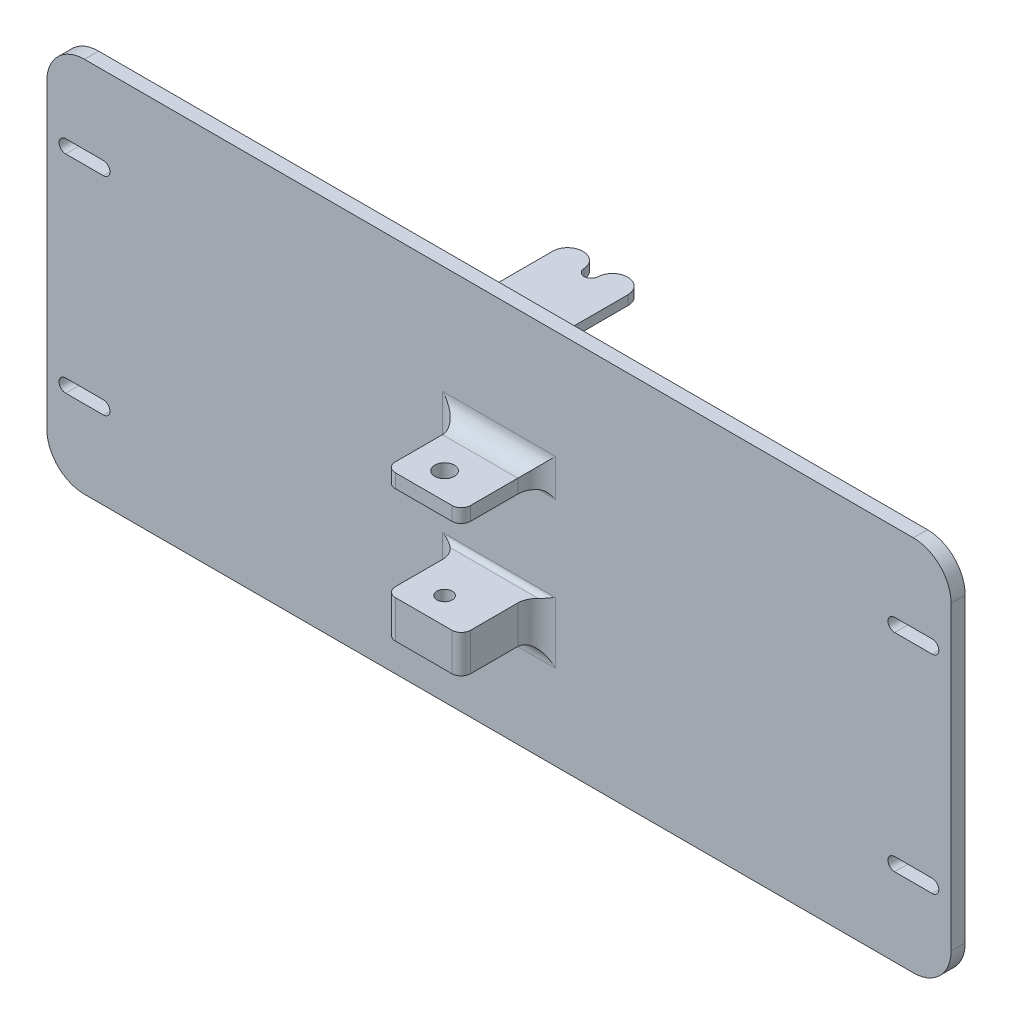
SolidWorks part; units mm, degrees
material "6061-T6 (SS)"
ref_plane "Front" through (0, 0, 0) normal (0, 0, 1) x (1, 0, 0)
ref_plane "Top" through (0, 0, 0) normal (0, 1, 0) x (1, 0, 0)
ref_plane "Right" through (0, 0, 0) normal (1, 0, 0) x (0, 0, -1)
sketch "Sketch1" plane through (0, 0, 0) normal (0, 0, 1) x (1, 0, 0)
  line L1 (-152.4, 63.5) -> (152.4, 63.5)
  line L2 (-152.4, 63.5) -> (-152.4, -63.5)
  line L3 (-152.4, -63.5) -> (152.4, -63.5)
  line L4 (152.4, 63.5) -> (152.4, -63.5)
  dimension "D1" = 152.4
  dimension "D2" = 304.8
  dimension "D3" = 63.5
  dimension "D4" = 127
extrude "Boss-Extrude1" add sketch "Sketch1" along normal blind 4.7625
sketch "Sketch2" plane through (0, 0, 0) normal (0, 0, -1) x (-1, 0, 0)
  line L0 (-12.7, 53.975) -> (12.7, 53.975) construction
  line L1 (0, 63.5) -> (0, -63.5) construction
  line L2 (-152.4, 63.5) -> (152.4, 63.5) construction
  line L3 (152.4, -63.5) -> (-152.4, -63.5) construction
  line L4 (-152.4, 0) -> (152.4, 0) construction
  line L5 (-12.7, 52.3875) -> (12.7, 52.3875)
  line L6 (-12.7, 52.3875) -> (-12.7, 55.5625)
  line L7 (-12.7, 55.5625) -> (12.7, 55.5625)
  line L8 (12.7, 52.3875) -> (12.7, 55.5625)
  line L9 (-152.4, -63.5) -> (-152.4, 63.5) construction
  line L10 (152.4, 63.5) -> (152.4, -63.5) construction
  line L11 (-12.7, -53.975) -> (12.7, -53.975) construction
  line L12 (12.7, -52.3875) -> (12.7, -55.5625)
  line L13 (-12.7, -55.5625) -> (12.7, -55.5625)
  line L14 (-12.7, -52.3875) -> (-12.7, -55.5625)
  line L15 (-12.7, -52.3875) -> (12.7, -52.3875)
  dimension "D1" = 3.175
  dimension "D2" = 25.4
  dimension "D3" = 12.7
  dimension "D4" = 53.975
extrude "Boss-Extrude2" add sketch "Sketch2" along normal blind 31.115
sketch "Sketch3" plane through (0, 0, 0) normal (0, 1, 0) x (1, 0, 0)
  line L0 (12.7, 31.115) -> (-12.7, 31.115) construction
  line L1 (0, 0) -> (0, 22.9508) construction
  line L2 (2.3813, 26.3525) -> (2.3813, 31.115)
  line L3 (2.3813, 31.115) -> (-2.3813, 31.115)
  line L4 (-2.3813, 31.115) -> (-2.3813, 26.3525)
  arc A1 (-2.3813, 26.3525) -> (2.3813, 26.3525) centre (0, 26.3525) ccw
  point P2 (0, 31.115)
  dimension "D2" = 2.3813
  dimension "D1" = 4.7625
  dimension "D3" = 4.7625
  dimension "D4" = 4.7625
extrude "Cut-Extrude1" cut sketch "Sketch3" against normal mid plane 127
fillet "Fillet1" radius 5.08 8 edges at (-2.3813, -53.975, -31.115) (2.3813, -53.975, -31.115) (-2.3813, 53.975, -31.115) (2.3813, 53.975, -31.115) (12.7, -53.975, -31.115) (-12.7, -53.975, -31.115) (-12.7, 53.975, -31.115) (12.7, 53.975, -31.115)
sketch "Sketch4" [suppressed] plane through (0, 0, 0) normal (0, 0, -1) x (-1, 0, 0)
  line L0 (0, 63.5) -> (0, -63.5) construction
  line L1 (-152.4, 63.5) -> (152.4, 63.5) construction
  line L2 (152.4, -63.5) -> (-152.4, -63.5) construction
  line L3 (-152.4, 0) -> (152.4, 0) construction
  line L4 (-60.325, 19.05) -> (-47.625, 19.05)
  line L5 (-60.325, 19.05) -> (-60.325, -19.05)
  line L6 (-60.325, -19.05) -> (-47.625, -19.05)
  line L7 (-47.625, 19.05) -> (-47.625, -19.05)
  line L8 (-152.4, -63.5) -> (-152.4, 63.5) construction
  line L9 (152.4, 63.5) -> (152.4, -63.5) construction
  line L10 (-53.975, 19.05) -> (-53.975, -19.05) construction
  line L11 (53.975, 19.05) -> (53.975, -19.05) construction
  line L12 (47.625, 19.05) -> (47.625, -19.05)
  line L13 (60.325, -19.05) -> (47.625, -19.05)
  line L14 (60.325, 19.05) -> (60.325, -19.05)
  line L15 (60.325, 19.05) -> (47.625, 19.05)
  dimension "D1" = 12.7
  dimension "D2" = 38.1
  dimension "D3" = 19.05
  dimension "D4" = 53.975
hole_wizard "#8-32 Tapped Hole1" positions "Sketch6" profile "Sketch5" tap size "#8-32" standard "Ansi Inch"
sketch "Sketch6" plane through (0, 0, 0) normal (0, 0, -1) x (-1, 0, 0)
  line L0 (-152.4, -63.5) -> (-152.4, 63.5) construction
  line L1 (-152.4, 63.5) -> (152.4, 63.5) construction
  point P0 (-139.7, 34.925)
  dimension "D1" = 12.7
  dimension "D2" = 28.575
sketch "Sketch5" plane through (139.7, 34.925, 0) normal (1, 0, 0) x (0, 1, 0)
  line L0 (0, 0) -> (0, 3.175)
  line L1 (0, 3.175) -> (1.7272, 3.175)
  line L2 (1.7272, 3.175) -> (1.7272, 0)
  line L5 (1.7272, 0) -> (0, 0)
  line L11 (0, -6.35) -> (0, 107.95) construction
  dimension "Thread Major Dia." = 3.4544
  dimension "Thru Tap Drill Depth" = 3.175
pattern_linear "LPattern1" [suppressed] count 2 spacing 279.4 count 2 spacing 69.85
fillet "Fillet2" radius 12.7 4 edges at (152.4, -63.5, 2.3813) (-152.4, -63.5, 2.3813) (-152.4, 63.5, 2.3813) (152.4, 63.5, 2.3813)
fillet "Fillet4" radius 6.35 8 edges at (12.7, -53.975, 0) (0, -52.3875, 0) (-12.7, -53.975, 0) (0, -55.5625, 0) (12.7, 53.975, 0) (0, 55.5625, 0) (-12.7, 53.975, 0) (0, 52.3875, 0)
sketch "Sketch7" plane through (0, 0, 0) normal (0, 0, -1) x (-1, 0, 0)
  line L0 (-146.05, 34.925) -> (-133.35, 34.925) construction
  line L1 (-146.05, 37.1475) -> (-133.35, 37.1475)
  line L2 (-146.05, 32.7025) -> (-133.35, 32.7025)
  line L4 (-139.7, 63.5) -> (139.7, 63.5) construction
  arc A0 (-146.05, 37.1475) -> (-146.05, 32.7025) centre (-146.05, 34.925) ccw
  arc A1 (-133.35, 32.7025) -> (-133.35, 37.1475) centre (-133.35, 34.925) ccw
  point P2 (-139.7, 34.925)
  dimension "D1" = 139.7
  dimension "D3" = 2.2225
  dimension "D2" = 28.575
  dimension "D4" = 12.7
extrude "Cut-Extrude2" cut sketch "Sketch7" against normal up to next (4.7625 mm away)
pattern_linear "LPattern2" count 2 spacing 279.4 along (-1, 0, 0) count 2 spacing 69.85 along (0, -1, 0) of "Cut-Extrude2"
sketch "Sketch8" plane through (0, 0, 4.7625) normal (0, 0, 1) x (1, 0, 0)
  line L0 (-152.4, 0) -> (152.4, 0) construction
  line L1 (-152.4, 50.8) -> (-152.4, -50.8) construction
  line L2 (152.4, -50.8) -> (152.4, 50.8) construction
  line L3 (0, -63.5) -> (0, 63.5) construction
  line L4 (-139.7, -63.5) -> (139.7, -63.5) construction
  line L5 (139.7, 63.5) -> (-139.7, 63.5) construction
  line L7 (-12.7, -28.5433) -> (12.7, -28.5433)
  line L8 (-12.7, -28.5433) -> (-12.7, -15.8432)
  line L9 (-12.7, -15.8432) -> (12.7, -15.8432)
  line L10 (12.7, -28.5433) -> (12.7, -15.8432)
  line L11 (-12.7, 15.9512) -> (12.7, 15.9512)
  line L12 (-12.7, 15.9512) -> (-12.7, 20.5867)
  line L13 (-12.7, 20.5867) -> (12.7, 20.5867)
  line L14 (12.7, 15.9512) -> (12.7, 20.5867)
  dimension "D1" = 12.7
  dimension "D2" = 4.6355
  dimension "D3" = 31.7944
  dimension "D4" = 15.8432
  dimension "D5" = 25.4
  dimension "D6" = 25.4
  dimension "D7" = 12.7
  dimension "D8" = 12.7
extrude "Boss-Extrude3" add sketch "Sketch8" along normal blind 25.4
sketch "Sketch9" plane through (0, 20.5867, 0) normal (0, 1, 0) x (1, 0, 0)
  line L1 (0, 0) -> (-7.8462, -62.3715) construction
  line L2 (12.7, -4.7625) -> (-12.7, -4.7625) construction
  line L4 (0.8497, -0.1069) -> (-6.9965, -62.4784) construction
  line L5 (12.7, -30.1625) -> (-12.7, -30.1625) construction
  circle A0 centre (-1.8129, -21.2725) radius 3.302
  dimension "D2" = 0.8564
  dimension "D1" = 8.89
  dimension "D4" = 6.604
  dimension "D3" = 97.17
extrude "Cut-Extrude3" cut sketch "Sketch9" against normal up to next
hole_wizard "13/64 (0.20313) Diameter Hole1" positions "Sketch11" profile "Sketch10" hole size "13/64" standard "Ansi Inch"
sketch "Sketch11" plane through (0, -15.8432, 0) normal (0, 1, 0) x (-1, 0, 0)
  line L0 (-12.7, 30.1625) -> (12.7, 30.1625) construction
  line L1 (-12.7, 30.1625) -> (-12.7, 4.7625) construction
  point P0 (1.8129, 21.2725)
  dimension "D1" = 8.89
  dimension "D2" = 14.5129
sketch "Sketch10" plane through (-1.8129, -15.8432, 21.2725) normal (1, 0, 0) x (0, 0, 1)
  line L0 (0, 0) -> (0, 10.6179)
  line L1 (0, 10.6179) -> (2.5798, 9.0678)
  line L2 (2.5798, 9.0678) -> (2.5798, 0)
  line L5 (2.5798, 0) -> (0, 0)
  line L10 (0, 10.6179) -> (-2.5798, 9.0678) construction
  line L11 (0, -6.35) -> (0, 107.95) construction
  dimension "Hole Dia." = 5.1595
  dimension "Hole Depth" = 9.0678
  dimension "Drill Angle" = 118
fillet "Fillet5" radius 6.35 4 edges at (12.7, -22.1933, 4.7625) (12.7, 18.269, 4.7625) (-12.7, 18.2689, 4.7625) (-12.7, -22.1932, 4.7625)
fillet "Fillet6" radius 3.175 4 edges at (-12.7, 18.2689, 30.1625) (12.7, 18.2689, 30.1625) (-12.7, -22.1932, 30.1625) (12.7, -22.1932, 30.1625)
fillet "Fillet7" radius 1.5875 2 edges at (0, 15.9512, 4.7625) (0, -15.8432, 4.7625)
sketch "Sketch12" plane through (0, 0, 4.7625) normal (0, 0, 1) x (1, 0, 0)
  line L0 (131.1275, 34.925) -> (88.0544, 34.925) construction
  line L1 (0, 0) -> (148.7518, 0) construction
  line L2 (152.4, -50.8) -> (152.4, 50.8) construction
  line L3 (107.95, 41.275) -> (120.65, 41.275)
  line L4 (107.95, 41.275) -> (107.95, 28.575)
  line L5 (107.95, 28.575) -> (120.65, 28.575)
  line L6 (120.65, 41.275) -> (120.65, 28.575)
  line L7 (107.95, -41.275) -> (107.95, -28.575)
  line L8 (107.95, -41.275) -> (120.65, -41.275)
  line L9 (120.65, -41.275) -> (120.65, -28.575)
  line L10 (107.95, -28.575) -> (120.65, -28.575)
  arc A0 (133.35, 37.1475) -> (133.35, 32.7025) centre (133.35, 34.925) ccw construction
  dimension "D1" = 12.7
  dimension "D2" = 6.35
  dimension "D3" = 31.75
  dimension "D4" = 12.7
extrude "Boss-Extrude4" [suppressed] add sketch "Sketch12" along normal blind 7.9375
hole_wizard "#17 (0.173) Diameter Hole1" positions "Sketch14" profile "Sketch13" hole size "#17" standard "Ansi Inch"
sketch "Sketch14" plane through (0, 0, 0) normal (0, 0, -1) x (-1, 0, 0)
  line L0 (-152.4, -50.8) -> (-152.4, 50.8) construction
  point P0 (-114.3, 34.925)
  dimension "D1" = 38.1
  dimension "D2" = 34.925
sketch "Sketch13" plane through (114.3, 34.925, 0) normal (1, 0, 0) x (0, 1, 0)
  line L0 (0, 0) -> (0, 10.7436)
  line L1 (0, 10.7436) -> (2.1971, 9.4234)
  line L2 (2.1971, 9.4234) -> (2.1971, 0)
  line L5 (2.1971, 0) -> (0, 0)
  line L10 (0, 10.7436) -> (-2.1971, 9.4234) construction
  line L11 (0, -6.35) -> (0, 107.95) construction
  dimension "Hole Dia." = 4.3942
  dimension "Hole Depth" = 9.4234
  dimension "Drill Angle" = 118
pattern_linear "LPattern3" [suppressed] count 2 spacing 69.85
fillet "Fillet8" [suppressed] radius 3.175
fillet "Fillet9" [suppressed] radius 3.175
fillet "Fillet10" [suppressed] radius 3.175
fillet "Fillet11" radius 6.35 2 edges at (0, -28.5433, 4.7625) (0, 20.5867, 4.7625)
